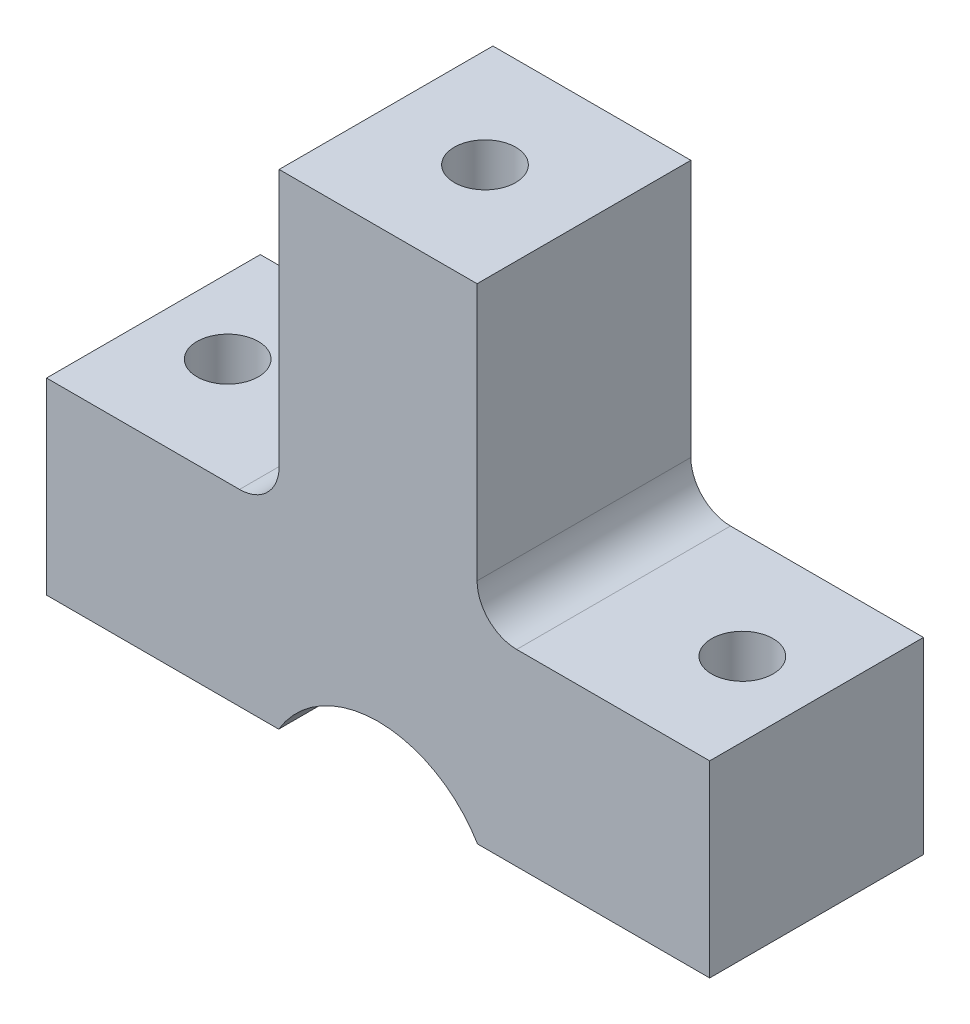
SolidWorks part; units mm, degrees
ref_plane "Front Plane" through (0, 0, 0) normal (0, 0, 1) x (1, 0, 0)
ref_plane "Top Plane" through (0, 0, 0) normal (0, 1, 0) x (1, 0, 0)
ref_plane "Right Plane" through (0, 0, 0) normal (1, 0, 0) x (0, 0, -1)
sketch "Sketch1" plane through (0, 0, 0) normal (0, 0, 1) x (1, 0, 0)
  line L4 (-12.35, 0) -> (-12.35, -9.5)
  line L5 (-12.35, -9.5) -> (21.15, -9.5)
  line L6 (21.15, -9.5) -> (21.15, 0)
  line L7 (21.15, 0) -> (-12.35, 0)
  line L8 (-12.35, 0) -> (-12.35, -9.5)
  line L9 (-12.35, -9.5) -> (21.15, -9.5)
  line L10 (21.15, -9.5) -> (21.15, 0)
  line L11 (21.15, 0) -> (-12.35, 0)
  dimension "D1" = 0
extrude "Boss-Extrude1" add sketch "Sketch1" along normal up to surface (10.8 mm away)
sketch "Sketch2" plane through (0, 0, 10.8) normal (0, 0, 1) x (1, 0, 0)
  arc A0 (-1.65, -12.5) -> (10.45, -12.5) centre (4.4, -12.5) ccw construction
  circle A1 centre (4.4, -12.5) radius 6.05
extrude "Cut-Extrude1" cut sketch "Sketch2" against normal up to surface (5 mm away)
sketch "Sketch4" plane through (0, 0, 5.8) normal (0, 0, 1) x (1, 0, 0)
  arc A0 (-3.65, -12.5) -> (12.45, -12.5) centre (4.4, -12.5) ccw construction
  circle A1 centre (4.4, -12.5) radius 8.05
extrude "Cut-Extrude2" cut sketch "Sketch4" against normal up to surface (3.8 mm away)
sketch "Sketch5" plane through (0, 0, 0) normal (0, 1, 0) x (1, 0, 0)
  circle A0 centre (17.4, -5.4) radius 1.55 construction
  circle A1 centre (-8.6, -5.4) radius 1.55 construction
  circle A2 centre (17.4, -5.4) radius 1.55
  circle A3 centre (-8.6, -5.4) radius 1.55
extrude "Cut-Extrude3" cut sketch "Sketch5" against normal through all
sketch "Sketch6" plane through (0, 0, 0) normal (0, 1, 0) x (1, 0, 0)
  line L0 (21.15, 0) -> (-12.35, 0) construction
  line L1 (-0.6, 0) -> (9.4, 0)
  line L2 (-0.6, 0) -> (-0.6, -10.8)
  line L3 (-0.6, -10.8) -> (9.4, -10.8)
  line L4 (9.4, 0) -> (9.4, -10.8)
  line L5 (-12.35, -10.8) -> (21.15, -10.8) construction
  line L6 (4.4, 0) -> (4.4, -10.8) construction
  line L7 (4.4, 64.0278) -> (4.4, -14.6278) construction
  dimension "D1" = 10
extrude "Boss-Extrude2" add sketch "Sketch6" along normal up to surface (15 mm away)
sketch "Sketch7" plane through (0, 15, 0) normal (0, 1, 0) x (1, 0, 0)
  line L0 (-0.6, -5.4) -> (9.4, -5.4) construction
  line L1 (-0.6, 0) -> (-0.6, -10.8) construction
  line L2 (9.4, -10.8) -> (9.4, 0) construction
  line L3 (4.4, 0) -> (4.4, -10.8) construction
  line L4 (9.4, 0) -> (-0.6, 0) construction
  line L5 (-0.6, -10.8) -> (9.4, -10.8) construction
  circle A0 centre (4.4, -5.4) radius 1.55
  dimension "D1" = 3.1
extrude "Cut-Extrude4" cut sketch "Sketch7" against normal blind 3
sketch "Sketch8" plane through (0, 12, 0) normal (0, 1, 0) x (1, 0, 0)
  line L0 (4.4, -5.4) -> (4.4, 0) construction
  line L1 (-0.6, 0) -> (9.4, 0)
  line L2 (1.55, 0) -> (7.25, 0)
  line L3 (1.55, -3.7546) -> (1.55, 0)
  line L4 (7.25, -7.0454) -> (7.25, -3.7546)
  line L5 (7.25, -3.7546) -> (4.4, -2.1091) construction
  line L6 (4.4, -2.1091) -> (1.55, -3.7546) construction
  line L7 (1.55, -3.7546) -> (1.55, -7.0454)
  line L8 (1.55, -7.0454) -> (4.4, -8.6909)
  line L9 (4.4, -8.6909) -> (7.25, -7.0454)
  line L10 (7.25, -3.7546) -> (7.25, 0)
  circle A0 centre (4.4, -5.4) radius 2.85 construction
  dimension "D1" = 5.7
extrude "Cut-Extrude5" cut sketch "Sketch8" against normal blind 2.75
fillet "Fillet1" radius 2 2 edges
sketch "Sketch9" plane through (0, 0, 10.8) normal (0, 0, 1) x (1, 0, 0)
  line L0 (9.6538, -9.5) -> (9.4222, -9.5)
  line L1 (-0.8538, -9.5) -> (-0.6222, -9.5)
  arc A0 (9.6538, -9.5) -> (-0.8538, -9.5) centre (4.4, -12.5) ccw construction
  arc A1 (9.6538, -9.5) -> (-0.8538, -9.5) centre (4.4, -12.5) ccw
  arc A2 (9.4222, -9.5) -> (-0.6222, -9.5) centre (4.4, -12.5) ccw
  arc A3 (9.4801, -9.5992) -> (-0.6801, -9.5992) centre (4.4, -12.5) ccw construction
  dimension "D1" = 0.2
extrude "Boss-Extrude3" add sketch "Sketch9" against normal up to surface (5 mm away) up to face at (4.4, -7.475, 5.8)
sketch "Sketch10" plane through (0, 0, 2) normal (0, 0, 1) x (1, 0, 0)
  line L0 (11.8701, -9.5) -> (11.6541, -9.5)
  line L1 (-3.0701, -9.5) -> (-2.8541, -9.5)
  line L2 (-3.0701, -9.5) -> (11.8701, -9.5) construction
  arc A0 (11.8701, -9.5) -> (-3.0701, -9.5) centre (4.4, -12.5) ccw construction
  arc A1 (11.8701, -9.5) -> (-3.0701, -9.5) centre (4.4, -12.5) ccw
  arc A2 (11.6541, -9.5) -> (-2.8541, -9.5) centre (4.4, -12.5) ccw
  arc A3 (11.6845, -9.5745) -> (-2.8845, -9.5745) centre (4.4, -12.5) ccw construction
  dimension "D1" = 0.2
extrude "Boss-Extrude4" add sketch "Sketch10" along normal up to next
